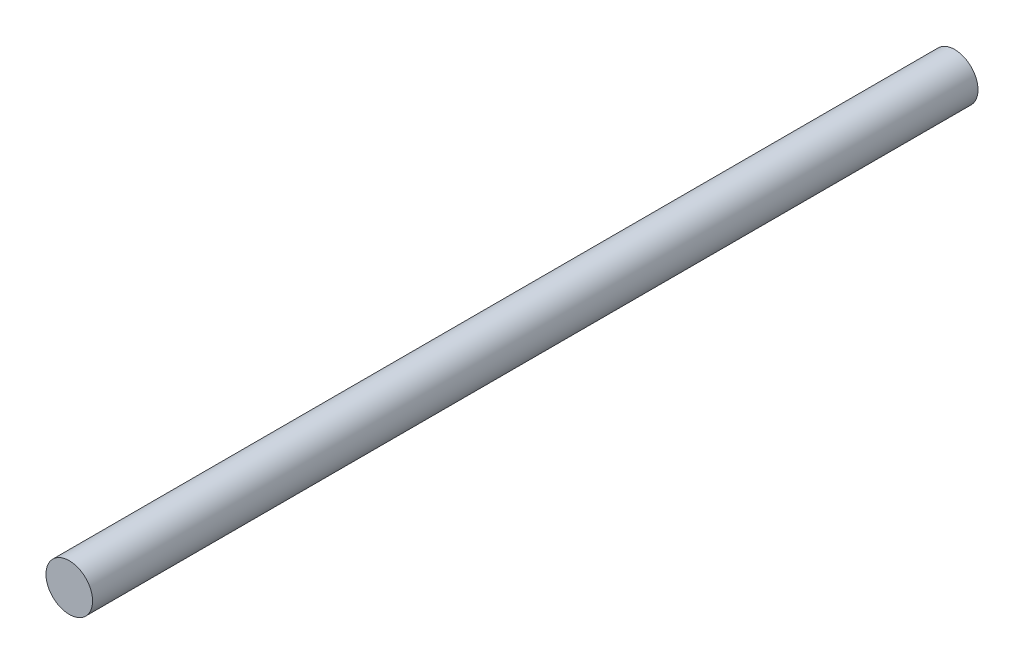
SolidWorks part; units mm, degrees
ref_plane "Front Plane" through (0, 0, 0) normal (0, 0, 1) x (1, 0, 0)
ref_plane "Top Plane" through (0, 0, 0) normal (0, 1, 0) x (1, 0, 0)
ref_plane "Right Plane" through (0, 0, 0) normal (1, 0, 0) x (0, 0, -1)
sketch "Sketch1" plane through (0, 0, 0) normal (0, 0, 1) x (1, 0, 0)
  circle A0 centre (0, 0) radius 5
extrude "Boss-Extrude1" add sketch "Sketch1" along normal blind 190
